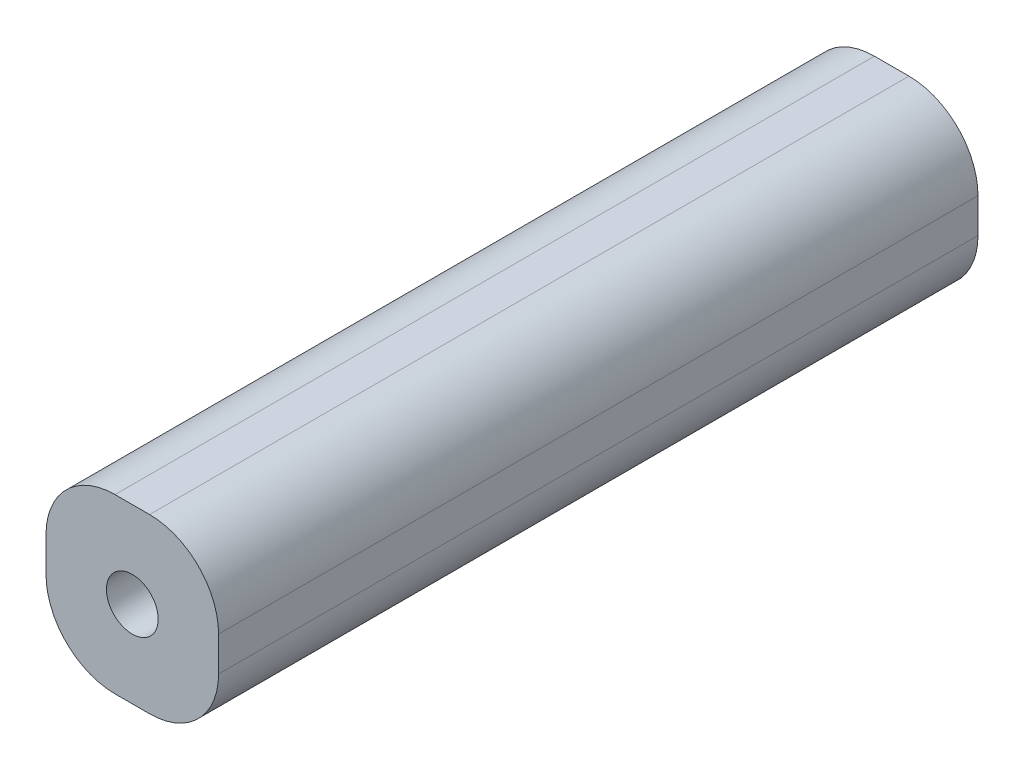
SolidWorks part; units mm, degrees
ref_plane "前视基准面" through (0, 0, 0) normal (0, 0, 1) x (1, 0, 0)
ref_plane "上视基准面" through (0, 0, 0) normal (0, 1, 0) x (1, 0, 0)
ref_plane "右视基准面" through (0, 0, 0) normal (1, 0, 0) x (0, 0, -1)
sketch "草图1" plane through (0, 0, 0) normal (0, 0, 1) x (1, 0, 0)
  line L1 (-6.28, 7.34) -> (3.72, 7.34)
  line L2 (-6.28, 7.34) -> (-6.28, -2.66)
  line L3 (-6.28, -2.66) -> (3.72, -2.66)
  line L4 (3.72, 7.34) -> (3.72, -2.66)
  line L5 (-6.28, 7.34) -> (3.72, -2.66) construction
  line L6 (-6.28, -2.66) -> (3.72, 7.34) construction
  circle A0 centre (-1.28, 2.34) radius 1.5
  point P0 (-1.28, 2.34)
  dimension "D1" = 10
  dimension "D2" = 10
extrude "凸台-拉伸1" add sketch "草图1" along normal blind 44
fillet "圆角1" radius 4 4 edges at (-6.28, -2.66, 22) (3.72, -2.66, 22) (3.72, 7.34, 22) (-6.28, 7.34, 22)
